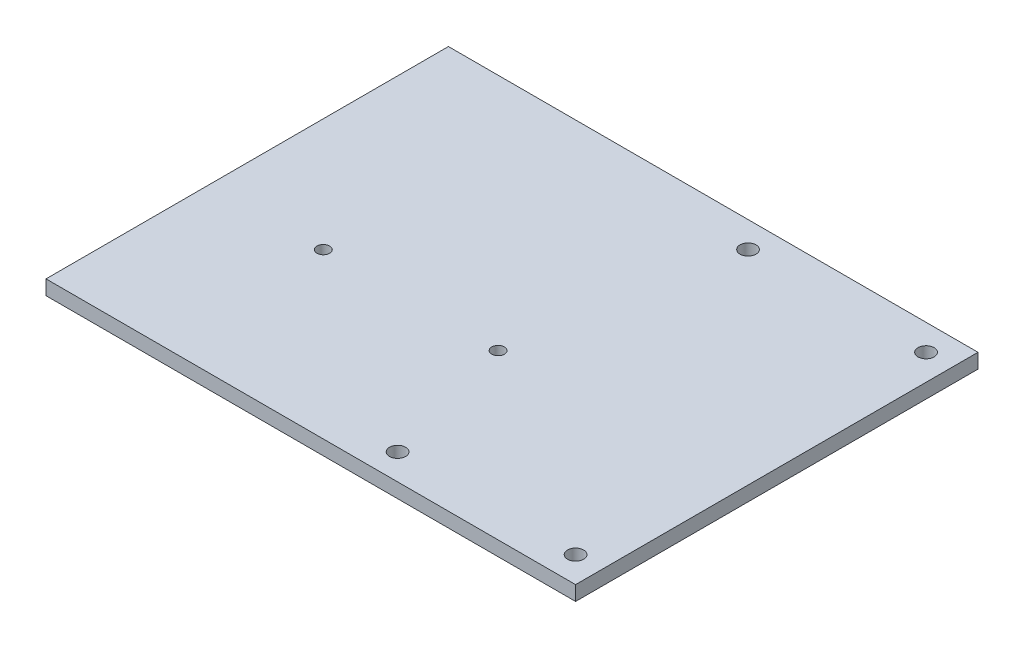
SolidWorks part; units mm, degrees
ref_plane "Front Plane" through (0, 0, 0) normal (0, 0, 1) x (1, 0, 0)
ref_plane "Top Plane" through (0, 0, 0) normal (0, 1, 0) x (1, 0, 0)
ref_plane "Right Plane" through (0, 0, 0) normal (1, 0, 0) x (0, 0, -1)
sketch "Sketch1" plane through (0, 0, 0) normal (0, 1, 0) x (1, 0, 0)
  line L0 (-11.3, -163.7) -> (-11.3, -11.3) construction
  line L1 (-230.3, 0) -> (0, 0)
  line L2 (-230.3, 0) -> (-230.3, -175)
  line L3 (-230.3, -175) -> (0, -175)
  line L4 (0, 0) -> (0, -175)
  circle A0 centre (-88.7, -163.7) radius 3.5
  circle A1 centre (-11.3, -163.7) radius 3.5
  circle A2 centre (-11.3, -11.3) radius 3.5
  circle A3 centre (-88.7, -11.3) radius 3.5
  circle A4 centre (-105, -103.7) radius 2.75
  circle A5 centre (-181, -103.7) radius 2.75
  point P13 (-11.3, -87.5)
  point P14 (0, -87.5)
  dimension "D3" = 7
  dimension "D4" = 77.4
  dimension "D5" = 152.4
  dimension "D7" = 5.5
  dimension "D1" = 175
  dimension "D2" = 49.3
  dimension "D6" = 11.3
  dimension "D8" = 60
  dimension "D9" = 16.3
  dimension "D10" = 76
extrude "Boss-Extrude1" add sketch "Sketch1" along normal blind 6.35
